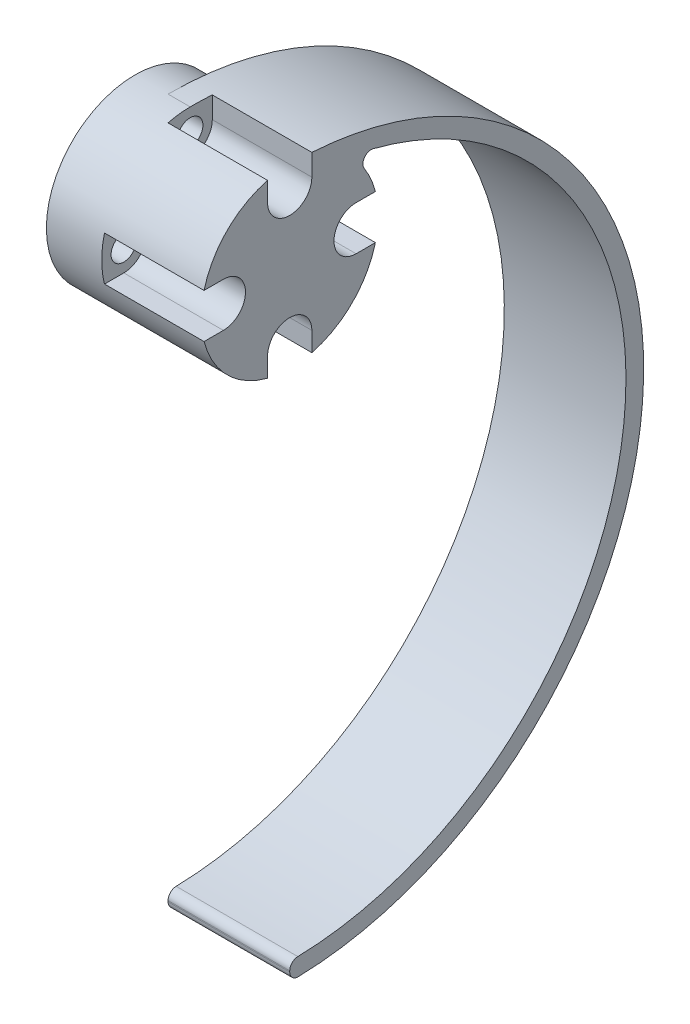
SolidWorks part; units mm, degrees
ref_plane "Front Plane" through (0, 0, 0) normal (0, 0, 1) x (1, 0, 0)
ref_plane "Top Plane" through (0, 0, 0) normal (0, 1, 0) x (1, 0, 0)
ref_plane "Right Plane" through (0, 0, 0) normal (1, 0, 0) x (0, 0, -1)
sketch "Hub-Sketch" plane through (0, 0, 0) normal (1, 0, 0) x (0, 0, -1)
  circle A0 centre (0, 0) radius 8
  circle A1 centre (0, 0) radius 6 construction
  circle A2 centre (0, 6) radius 1.15
  circle A3 centre (-6, 0) radius 1.15
  circle A4 centre (0, -6) radius 1.15
  circle A5 centre (6, 0) radius 1.15
  dimension "D1" = 16
  dimension "D2" = 12
  dimension "D3" = 2.3
extrude "Hub" add sketch "Hub-Sketch" against normal blind 3 and the other way blind 11
sketch "Leg-Sketch" plane through (11, 0, 0) normal (1, 0, 0) x (0, 0, -1)
  line L0 (0, -56) -> (0, -54.4)
  circle A1 centre (0, 0) radius 8 construction
  arc A2 (0, 8) -> (0, -56) centre (0, -24) cw
  arc A3 (5.3809, 5.92) -> (0, -54.4) centre (0, -24) cw
  arc A4 (0, 8) -> (5.3809, 5.92) centre (0, 0) cw
  dimension "D1" = 32
  dimension "D2" = 1.6
extrude "Leg" add sketch "Leg-Sketch" against normal up to surface (11 mm away) up to plane "Right Plane"
sketch "Clearance-Sketch" plane through (11, 0, 0) normal (1, 0, 0) x (0, 0, -1)
  line L8 (-2, 8) -> (2, 8)
  line L9 (2, 8) -> (2, 6)
  line L10 (-2, 6) -> (-2, 8)
  line L11 (8, 2) -> (8, -2)
  line L12 (8, -2) -> (6, -2)
  line L13 (6, 2) -> (8, 2)
  line L14 (2, -8) -> (-2, -8)
  line L15 (-2, -8) -> (-2, -6)
  line L16 (2, -6) -> (2, -8)
  line L17 (-8, -2) -> (-8, 2)
  line L18 (-8, 2) -> (-6, 2)
  line L19 (-6, -2) -> (-8, -2)
  arc A0 (6, -2) -> (6, 2) centre (6, 0) cw
  arc A3 (-2, -6) -> (2, -6) centre (0, -6) cw
  arc A10 (2, 6) -> (-2, 6) centre (0, 6) cw
  circle A11 centre (0, 6) radius 1.15 construction
  circle A12 centre (0, 0) radius 8 construction
  arc A13 (-6, 2) -> (-6, -2) centre (-6, 0) cw
  point P27 (0, 0)
  dimension "D1" = 2
extrude "Clearance" cut sketch "Clearance-Sketch" against normal offset from surface (9 mm away) 5 up to face at (-3, 0, -7.15)
fillet "Fillet" radius 0.75 3 edges at (5.5, 5.92, -5.3809) (5.5, -54.4, 0) (5.5, -56, 0)
mirror "Mirror" [suppressed] about plane through (0, 0, 0) normal (1, 0, 0)
delete or keep bodies "KeepMirrorBody" [suppressed] type keep bodies bodies 104
equation "\"LEG_CLEARANCE\"= 3mm"
equation "\"LEG_WIDTH\"= 11mm"
equation "\"LEG_THICKNESS\"= 1.6mm"
equation "\"LEG_DIAMETER\"= 64mm"
equation "\"D1@Hub\"=\"HUB_WIDTH\""
equation "\"D2@Hub\"=\"LEG_WIDTH\""
equation "\"D2@Leg-Sketch\"=\"LEG_THICKNESS\""
equation "\"D1@Leg-Sketch\"=\"LEG_DIAMETER\"/2"
equation "\"HUB_WIDTH\"= \"LEG_CLEARANCE\""
